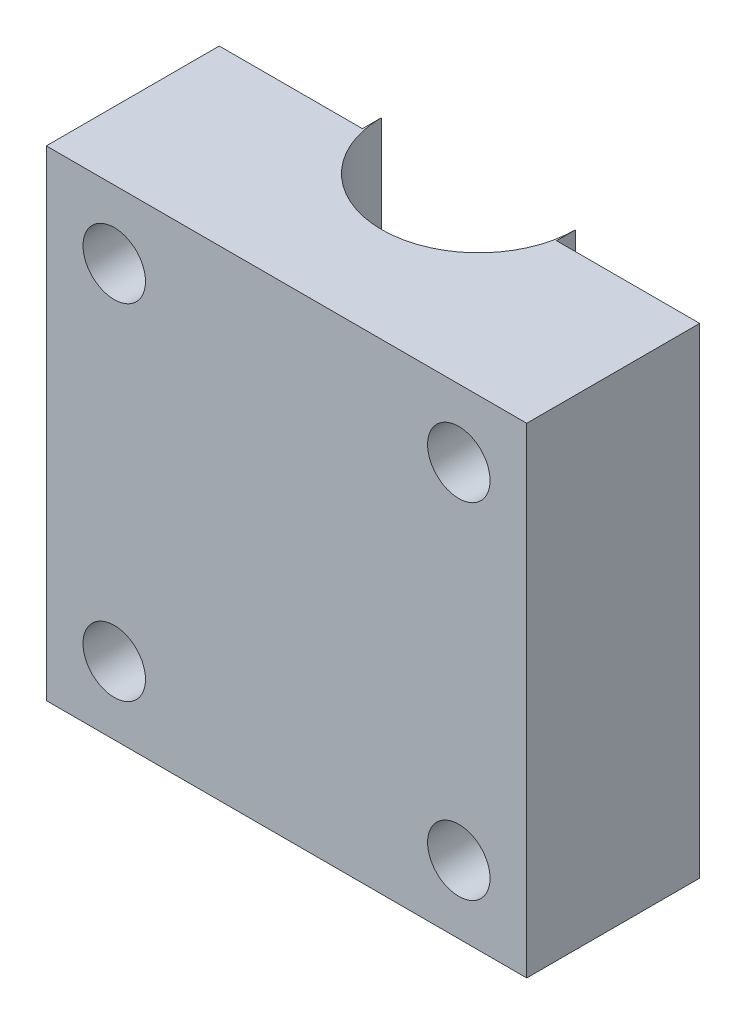
SolidWorks part; units mm, degrees
ref_plane "Front Plane" through (0, 0, 0) normal (0, 0, 1) x (1, 0, 0)
ref_plane "Top Plane" through (0, 0, 0) normal (0, 1, 0) x (1, 0, 0)
ref_plane "Right Plane" through (0, 0, 0) normal (1, 0, 0) x (0, 0, -1)
sketch "Sketch1" plane through (0, 0, 0) normal (0, 0, 1) x (1, 0, 0)
  line L1 (-12.5, -12.5) -> (12.5, -12.5)
  line L2 (-12.5, -12.5) -> (-12.5, 12.5)
  line L3 (-12.5, 12.5) -> (12.5, 12.5)
  line L4 (12.5, -12.5) -> (12.5, 12.5)
  line L5 (-12.5, -12.5) -> (12.5, 12.5) construction
  line L6 (-12.5, 12.5) -> (12.5, -12.5) construction
  point P0 (0, 0)
  dimension "D1" = 25
  dimension "D2" = 25
extrude "Boss-Extrude2" add sketch "Sketch1" along normal blind 10
sketch "Sketch2" plane through (0, 12.5, 0) normal (0, 1, 0) x (1, 0, 0)
  line L0 (12.5, 0) -> (-12.5, 0) construction
  circle A0 centre (0, 0) radius 5.05
  dimension "D1" = 10.1
extrude "Cut-Extrude1" cut sketch "Sketch2" against normal through all
sketch "Sketch3" plane through (0, 0, 10) normal (0, 0, 1) x (1, 0, 0)
  line L0 (-12.5, 12.5) -> (-8.9645, 8.9645) construction
  line L1 (12.5, 12.5) -> (8.9645, 8.9645) construction
  line L2 (12.5, -12.5) -> (8.9645, -8.9645) construction
  line L3 (-12.5, -12.5) -> (-8.9645, -8.9645) construction
  circle A0 centre (-8.9645, 8.9645) radius 1.625
  circle A1 centre (8.9645, 8.9645) radius 1.625
  circle A2 centre (8.9645, -8.9645) radius 1.625
  circle A3 centre (-8.9645, -8.9645) radius 1.625
  dimension "D5" = 3.25
  dimension "D6" = 3.25
  dimension "D7" = 3.25
  dimension "D8" = 3.25
  dimension "D1" = 5
  dimension "D2" = 5
  dimension "D3" = 5
  dimension "D4" = 5
extrude "Cut-Extrude2" cut sketch "Sketch3" against normal through all
sketch "Sketch4" plane through (0, 0, 0) normal (0, 0, -1) x (-1, 0, 0)
  line L1 (-12.5, 12.5) -> (-5.05, 12.5)
  line L2 (-12.5, 12.5) -> (-12.5, -12.5)
  line L3 (-12.5, -12.5) -> (-5.05, -12.5)
  line L4 (-5.05, 12.5) -> (-5.05, -12.5)
  line L5 (5.05, 12.5) -> (12.5, 12.5)
  line L6 (5.05, 12.5) -> (5.05, -12.5)
  line L7 (5.05, -12.5) -> (12.5, -12.5)
  line L8 (12.5, 12.5) -> (12.5, -12.5)
extrude "Cut-Extrude3" cut sketch "Sketch4" against normal blind 1
